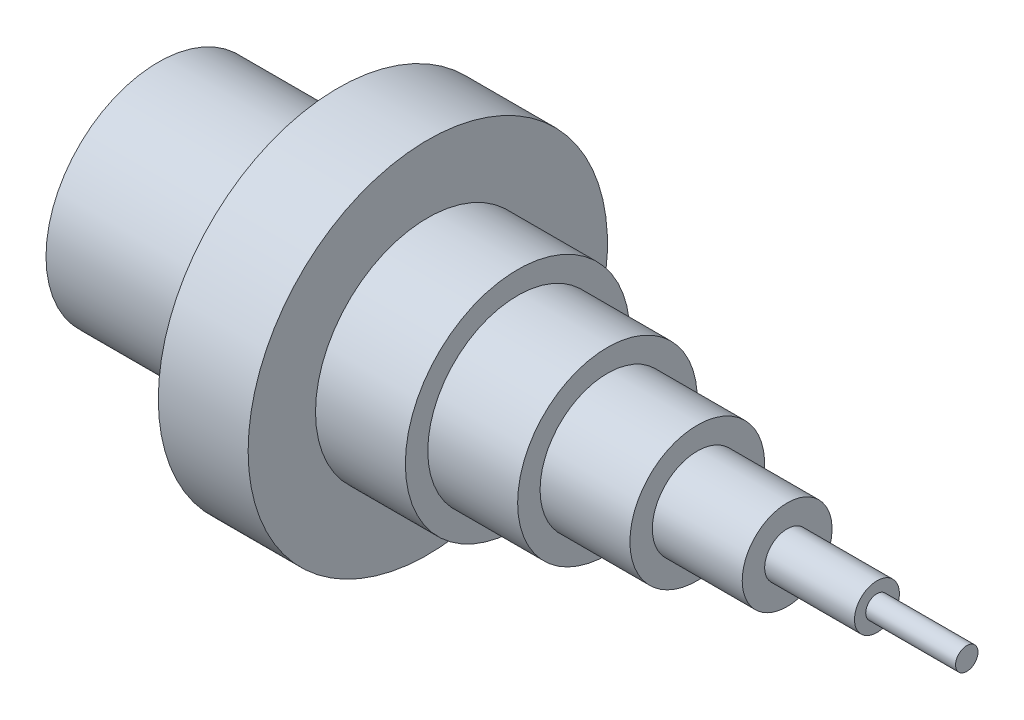
SolidWorks part; units mm, degrees
ref_plane "Front Plane" through (0, 0, 0) normal (0, 0, 1) x (1, 0, 0)
ref_plane "Top Plane" through (0, 0, 0) normal (0, 1, 0) x (1, 0, 0)
ref_plane "Right Plane" through (0, 0, 0) normal (1, 0, 0) x (0, 0, -1)
sketch "Sketch1" plane through (0, 0, 0) normal (0, 0, 1) x (1, 0, 0)
  line L0 (-116.6667, 0) -> (116.5138, 0) construction
  line L1 (0, 0) -> (0, 25)
  line L2 (0, 25) -> (40, 25)
  line L3 (40, 25) -> (40, 40)
  line L4 (40, 40) -> (60, 40)
  line L5 (60, 40) -> (60, 25)
  line L6 (60, 25) -> (80, 25)
  line L7 (80, 25) -> (80, 20)
  line L8 (80, 20) -> (100, 20)
  line L9 (100, 20) -> (100, 15)
  line L10 (100, 15) -> (120, 15)
  line L11 (120, 15) -> (120, 10)
  line L12 (120, 10) -> (140, 10)
  line L13 (140, 10) -> (140, 5)
  line L14 (140, 5) -> (160, 5)
  line L15 (160, 5) -> (160, 2.5)
  line L16 (160, 2.5) -> (180, 2.5)
  line L17 (180, 2.5) -> (180, 0)
  line L18 (180, 0) -> (0, 0)
  dimension "D1" = 50
  dimension "D2" = 40
  dimension "D3" = 80
  dimension "D4" = 50
  dimension "D5" = 180
  dimension "D6" = 20
  dimension "D7" = 40
  dimension "D8" = 20
  dimension "D9" = 30
  dimension "D10" = 20
  dimension "D11" = 20
  dimension "D12" = 20
  dimension "D13" = 20
  dimension "D14" = 20
  dimension "D15" = 10
  dimension "D16" = 5
revolve "Revolve1" add sketch "Sketch1" angle 360 about L0
sketch "Sketch2" plane through (0, 0, 0) normal (-1, 0, 0) x (0, 0, 1)
  circle A0 centre (0, 0) radius 20
  dimension "D1" = 40
extrude "Cut-Extrude1" cut sketch "Sketch2" against normal blind 40
